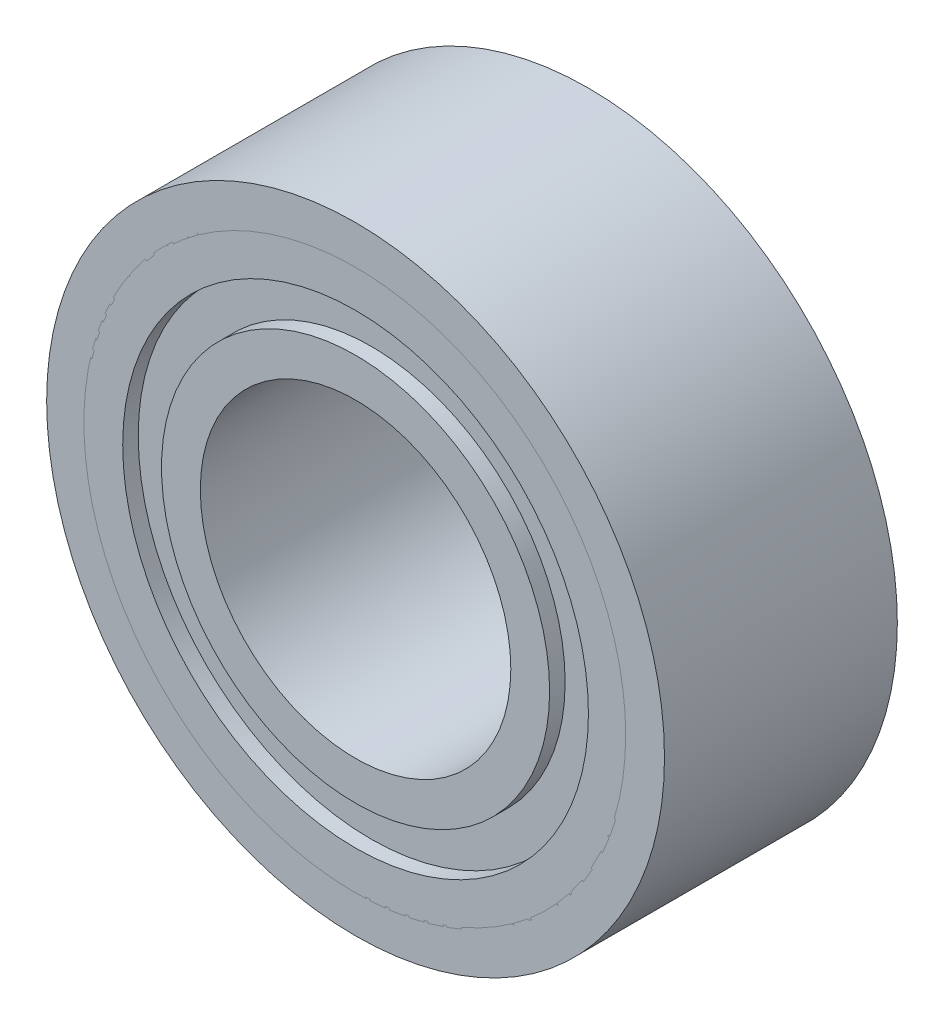
SolidWorks part; units mm, degrees
ref_plane "Front Plane" through (0, 0, 0) normal (0, 0, 1) x (1, 0, 0)
ref_plane "Top Plane" through (0, 0, 0) normal (0, 1, 0) x (1, 0, 0)
ref_plane "Right Plane" through (0, 0, 0) normal (1, 0, 0) x (0, 0, -1)
sketch "Sketch1" plane through (0, 0, 0) normal (0, 0, 1) x (1, 0, 0)
  circle A0 centre (0, 0) radius 3.98
  circle A1 centre (0, 0) radius 2
  dimension "D1" = 4
  dimension "D2" = 7.96
extrude "Boss-Extrude1" add sketch "Sketch1" along normal blind 3
sketch "Sketch2" plane through (0, 0, 3) normal (0, 0, 1) x (1, 0, 0)
  circle A3 centre (0, 0) radius 3.48
  circle A4 centre (0, 0) radius 3.98 construction
  circle A5 centre (0, 0) radius 2.5
  circle A6 centre (0, 0) radius 2 construction
  dimension "D1" = 0.5
  dimension "D2" = 0.5
extrude "Cut-Extrude1" cut sketch "Sketch2" against normal blind 3
sketch "Sketch3" plane through (0, 0, 3) normal (0, 0, 1) x (1, 0, 0)
  circle A0 centre (0, 0) radius 2.5
  circle A1 centre (0, 0) radius 3.5
  dimension "D1" = 5
  dimension "D2" = 7
extrude "Boss-Extrude3" add sketch "Sketch3" against normal blind 2.8 separate body
sketch "Sketch4" plane through (0, 0, 3) normal (0, 0, 1) x (1, 0, 0)
  circle A0 centre (0, 0) radius 2
  circle A1 centre (0, 0) radius 3
extrude "Cut-Extrude2" cut sketch "Sketch4" against normal blind 0.2
